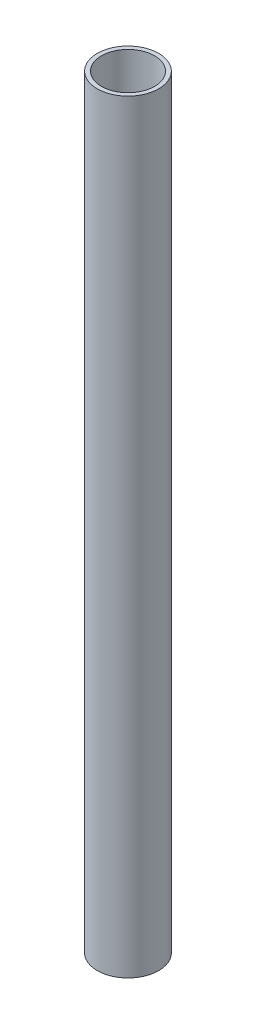
SolidWorks part; units mm, degrees
ref_plane "Front Plane" through (0, 0, 0) normal (0, 0, 1) x (1, 0, 0)
ref_plane "Top Plane" through (0, 0, 0) normal (0, 1, 0) x (1, 0, 0)
ref_plane "Right Plane" through (0, 0, 0) normal (1, 0, 0) x (0, 0, -1)
sketch "Sketch1" plane through (0, 0, 0) normal (0, 1, 0) x (1, 0, 0)
  circle A0 centre (0, 0) radius 18.5
  circle A1 centre (0, 0) radius 16
  dimension "D1" = 37
  dimension "D2" = 32
extrude "Boss-Extrude1" add sketch "Sketch1" along normal blind 460 contours A1 | A0
ref_point "Point1"
equation "\"D1@Boss-Extrude1\"=380+80"
